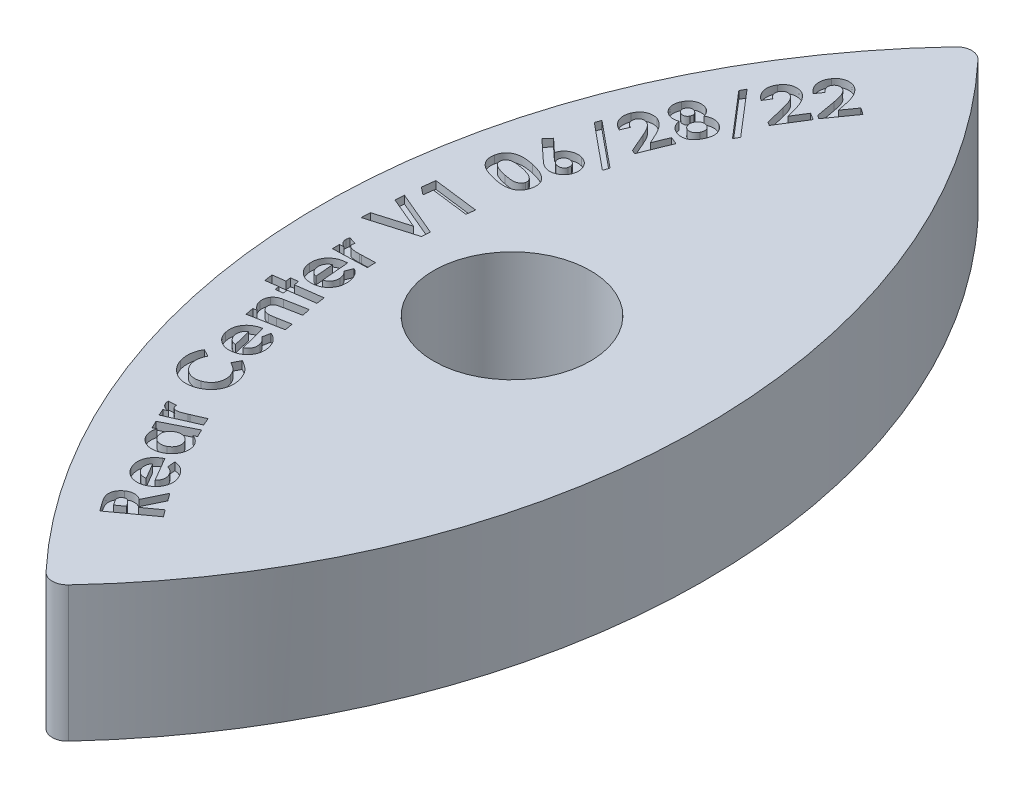
SolidWorks part; units mm, degrees
ref_plane "Front Plane" through (0, 0, 0) normal (0, 0, 1) x (1, 0, 0)
ref_plane "Top Plane" through (0, 0, 0) normal (0, 1, 0) x (1, 0, 0)
ref_plane "Right Plane" through (0, 0, 0) normal (1, 0, 0) x (0, 0, -1)
sketch "Sketch2" plane through (0, 0, 0) normal (1, 0, 0) x (0, 0, -1)
  line L0 (-15.7391, 19.787) -> (12.7788, 17.9806) construction
  line L1 (-38.1, -0.1139) -> (-38.1, 11.1125)
  line L2 (-38.1, 11.1125) -> (38.1, 11.1125)
  line L3 (38.1, 11.1125) -> (38.1, -0.2597)
  line L4 (-38.1, 0) -> (38.1, 0) construction
  line L5 (-302.918, -43.2315) -> (-283.9965, -45.4399) construction
  line L6 (-9.9515, 0.403) -> (9.0957, 0.7277) construction
  spline S0 degree 2 poles (-38.1, -0.1139) (0.0007, 0.1868) (38.1, -0.2597) knots 0 0 0 1 1 1
  point P4 (0, -3.7491)
  dimension "D1" = 28.575
  dimension "D2" = 11.1125
  dimension "D3" = 19.05
  dimension "D4" = 76.2
  dimension "D5" = 19.05
extrude "Boss-Extrude1" add sketch "Sketch2" against normal mid plane 31.75
sketch "Sketch3" plane through (0, 11.1125, 0) normal (0, 1, 0) x (1, 0, 0)
  line L0 (-15.875, 38.1) -> (-15.875, -38.1) construction
  line L1 (0, 0) -> (0, 38.1) construction
  line L2 (-15.875, 38.1) -> (15.875, 38.1) construction
  line L3 (15.875, 38.1) -> (15.875, -38.1) construction
  line L4 (-15.875, -38.1) -> (15.875, -38.1) construction
  line L9 (15.875, -38.1) -> (15.875, 38.1)
  line L10 (15.875, 38.1) -> (-15.875, 38.1)
  line L11 (-15.875, 38.1) -> (-15.875, -38.1)
  line L12 (-15.875, -38.1) -> (15.875, -38.1)
  line L13 (15.875, -38.1) -> (15.875, 38.1)
  line L14 (15.875, 38.1) -> (-15.875, 38.1)
  line L15 (-15.875, 38.1) -> (-15.875, -38.1)
  line L16 (-15.875, -38.1) -> (15.875, -38.1)
  arc A0 (-0.9249, 37.7004) -> (-0.9249, -37.7004) centre (39.1353, 0) ccw
  arc A1 (0.9249, 37.7004) -> (0.9249, -37.7004) centre (-39.1353, 0) cw
  arc A2 (0.9249, 37.7004) -> (-0.9249, 37.7004) centre (0, 36.83) ccw
  arc A3 (0.9249, -37.7004) -> (-0.9249, -37.7004) centre (0, -36.83) cw
  circle A4 centre (0, 0) radius 6.5
  dimension "D1" = 1.27
  dimension "D3" = 13
  dimension "D2" = 0
extrude "Cut-Extrude1" cut sketch "Sketch3" against normal through all
sketch "Sketch5" plane through (0, 11.1125, 0) normal (0, 1, 0) x (1, 0, 0)
  arc A2 (3.6994, 33.3485) -> (3.6994, -33.3485) centre (39.1353, 0) ccw
  arc A3 (3.6138, 33.2573) -> (3.6994, -33.3485) centre (39.1353, 0) ccw
  dimension "D1" = 6.35
sketch "Sketch6" plane through (0, 11.1125, 0) normal (0, 1, 0) x (1, 0, 0)
  text T0 "<b>Rear Center V1 06/28/22</b>" font "Century Gothic" height 3.81
extrude "Cut-Extrude2" cut sketch "Sketch6" against normal blind 0.635
